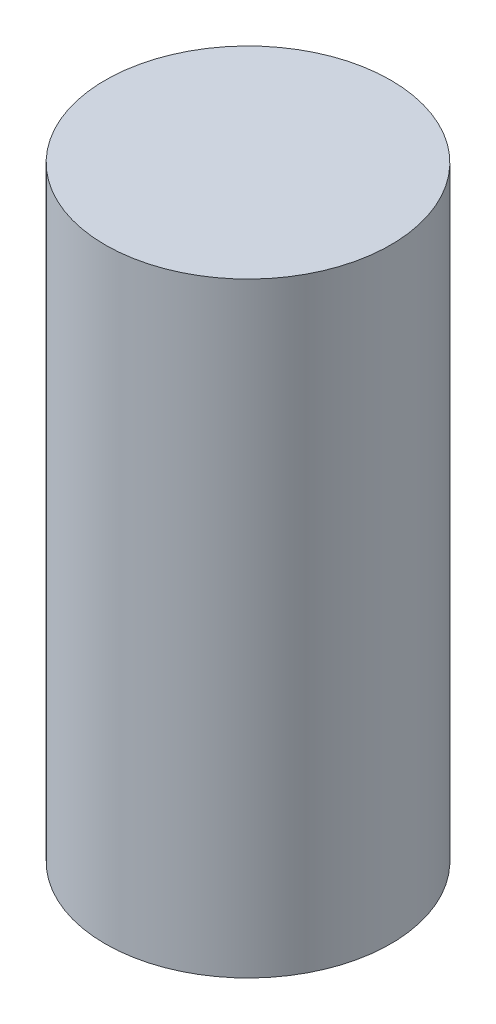
SolidWorks part; units mm, degrees
ref_plane "Front Plane" through (0, 0, 0) normal (0, 0, 1) x (1, 0, 0)
ref_plane "Top Plane" through (0, 0, 0) normal (0, 1, 0) x (1, 0, 0)
ref_plane "Right Plane" through (0, 0, 0) normal (1, 0, 0) x (0, 0, -1)
sketch "Sketch2" plane through (0, 0, 0) normal (0, 1, 0) x (1, 0, 0)
  circle A0 centre (0, 0) radius 31.75
  dimension "D1" = 63.5
extrude "Boss-Extrude1" add sketch "Sketch2" along normal blind 134.62
